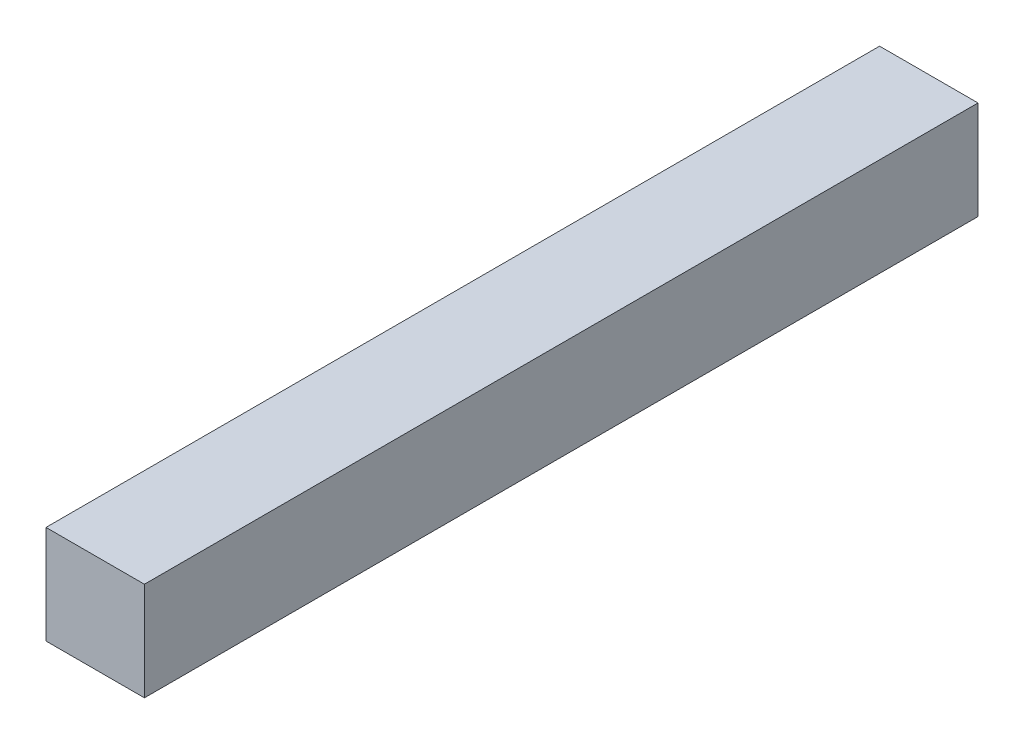
SolidWorks part; units mm, degrees
ref_plane "Front Plane" through (0, 0, 0) normal (0, 0, 1) x (1, 0, 0)
ref_plane "Top Plane" through (0, 0, 0) normal (0, 1, 0) x (1, 0, 0)
ref_plane "Right Plane" through (0, 0, 0) normal (1, 0, 0) x (0, 0, -1)
sketch "Sketch2" plane through (0, 0, 0) normal (0, 0, 1) x (1, 0, 0)
  line L1 (0, 0) -> (3, 0)
  line L2 (0, 0) -> (0, 3)
  line L3 (0, 3) -> (3, 3)
  line L4 (3, 0) -> (3, 3)
extrude "Boss-Extrude1" add sketch "Sketch2" along normal blind 25.41
